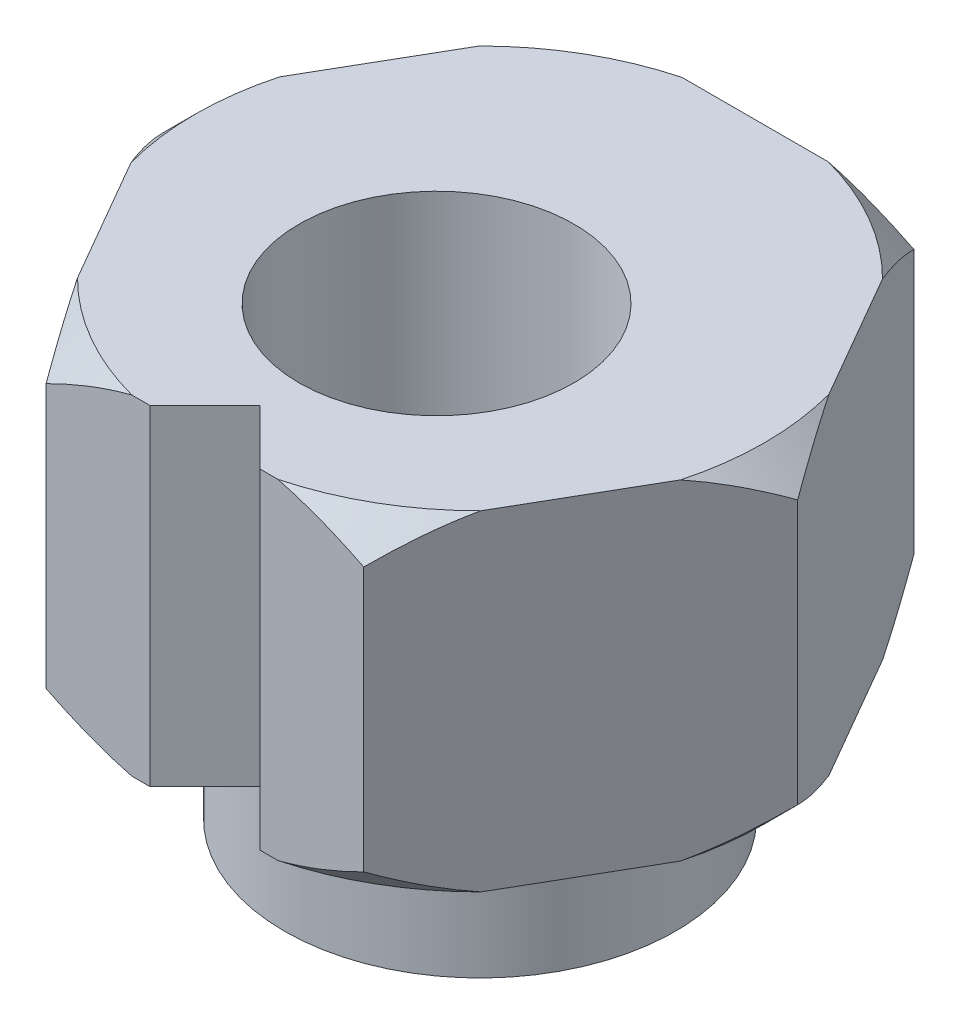
SolidWorks part; units mm, degrees
material "AISI 304"
ref_plane "Front Plane" through (0, 0, 0) normal (0, 0, 1) x (1, 0, 0)
ref_plane "Top Plane" through (0, 0, 0) normal (0, 1, 0) x (1, 0, 0)
ref_plane "Right Plane" through (0, 0, 0) normal (1, 0, 0) x (0, 0, -1)
sketch "Sketch1" plane through (0, 0, 0) normal (0, 1, 0) x (1, 0, 0)
  line L1 (5.7735, 0) -> (2.8868, 5)
  line L2 (2.8868, 5) -> (-2.8868, 5)
  line L3 (-2.8868, 5) -> (-5.7735, 0)
  line L4 (-5.7735, 0) -> (-2.8868, -5)
  line L5 (-2.8868, -5) -> (2.8868, -5)
  line L6 (2.8868, -5) -> (5.7735, 0)
  circle A0 centre (0, 0) radius 5 construction
  dimension "D1" = 10
extrude "Boss-Extrude1" add sketch "Sketch1" along normal blind 6
sketch "Sketch3" plane through (0, 0, 0) normal (0, -1, 0) x (1, 0, 0)
  circle A0 centre (0, 0) radius 3.555
  dimension "D1" = 7.11
extrude "Boss-Extrude3" add sketch "Sketch3" along normal blind 2.5
sketch "Sketch4" plane through (0, 6, 0) normal (0, 1, 0) x (1, 0, 0)
  line L0 (0, 0) -> (0, -0.79) construction
  circle A0 centre (0, -0.79) radius 2.5
  dimension "D1" = 5
  dimension "D2" = 0.79
extrude "Cut-Extrude1" cut sketch "Sketch4" against normal through all
sketch "Sketch5" plane through (0, 0, 0) normal (0, -1, 0) x (-1, 0, 0)
  line L0 (2.8868, -5) -> (-2.8868, -5) construction
  line L1 (-1, -5) -> (1, -5)
  line L2 (-1, -5) -> (0, -4)
  line L4 (1, -5) -> (0, -4)
  line L5 (0, -5) -> (0, 0) construction
  dimension "D1" = 2
extrude "Cut-Extrude2" cut sketch "Sketch5" against normal through all
sketch "Sketch6" plane through (0, 0, 0) normal (0, 0, 1) x (1, 0, 0)
  line L0 (0, 0) -> (0, 6.4706) construction
  line L1 (5.1735, 6) -> (5.7735, 6)
  line L2 (2.8868, 6) -> (5.7735, 6) construction
  line L3 (5.7735, 6) -> (5.7735, 5.4)
  line L4 (5.7735, 6) -> (5.7735, 0) construction
  line L5 (5.7735, 5.4) -> (5.1735, 6)
  line L6 (5.7735, 3) -> (6.8775, 3) construction
  line L7 (5.7735, 6) -> (5.7735, 0) construction
  line L8 (5.7735, 0.6) -> (5.1735, 0)
  line L9 (5.7735, 0) -> (5.7735, 0.6)
  line L10 (5.1735, 0) -> (5.7735, 0)
  dimension "D1" = 0.6
revolve "Cut-Revolve1" cut sketch "Sketch6" angle 360 about L0
